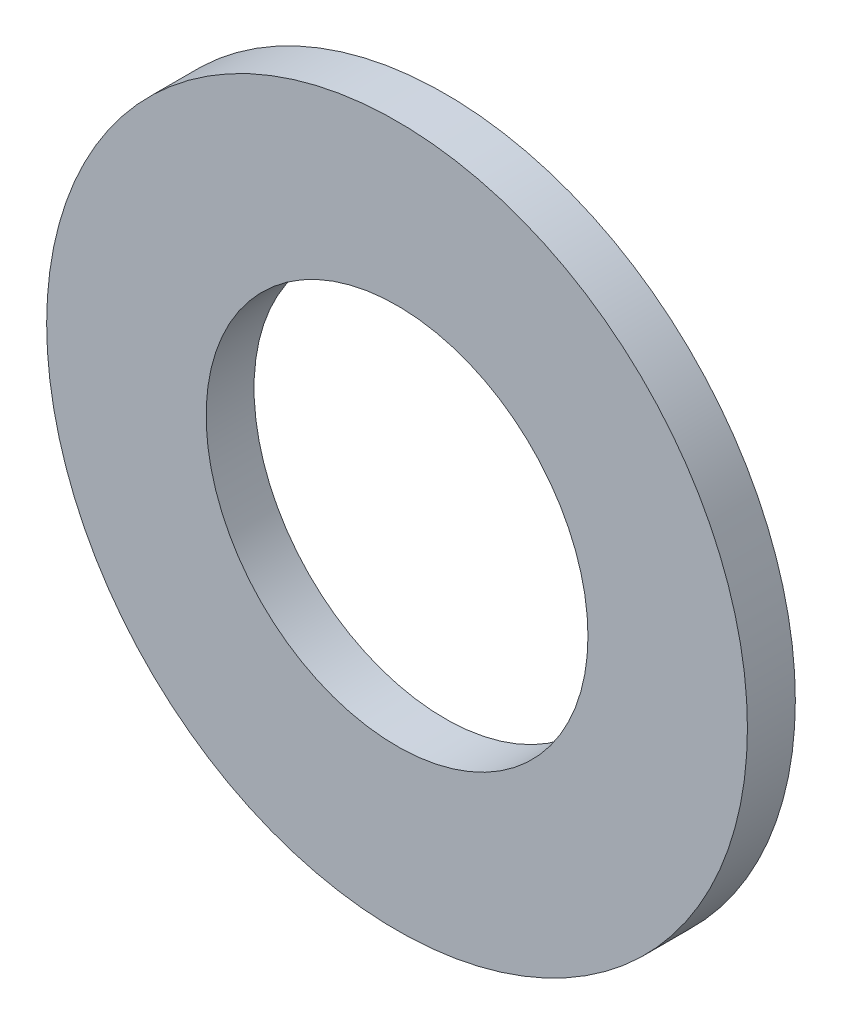
SolidWorks part; units mm, degrees
ref_plane "Front Plane" through (0, 0, 0) normal (0, 0, 1) x (1, 0, 0)
ref_plane "Top Plane" through (0, 0, 0) normal (0, 1, 0) x (1, 0, 0)
ref_plane "Right Plane" through (0, 0, 0) normal (1, 0, 0) x (0, 0, -1)
sketch "Sketch1" plane through (0, 0, 0) normal (0, 0, 1) x (1, 0, 0)
  line L0 (-5.9436, 0) -> (5.9436, 0) construction
  line L1 (0, -5.9436) -> (0, 5.9436) construction
  circle A0 centre (0, 0) radius 5.9436
  circle A1 centre (0, 0) radius 3.2385
  point P4 (0, 0)
  point P9 (0, 0)
  dimension "ID" = 6.477
  dimension "OD" = 11.8872
sketch "Sketch2" plane through (0, 0, 0) normal (1, 0, 0) x (0, 0, -1)
  line L0 (0.4064, 5.9436) -> (-0.4064, 5.9436) construction
  line L1 (0, 5.9436) -> (0, -5.9436) construction
  point P4 (0, 5.9436)
  dimension "Thickness" = 0.8128
sketch "Sketch3" plane through (0, 0, 0) normal (0, 0, 1) x (1, 0, 0)
  line L0 (0, -5.9436) -> (0, 5.9436) construction
  circle A0 centre (0, 0) radius 5.9436
  circle A1 centre (0, 0) radius 3.2385
  circle A2 centre (0, 0) radius 3.2385 construction
extrude "Boss-Extrude1" add sketch "Sketch3" along normal mid plane 0.8128
equation "\"D1@Boss-Extrude1\" = \"Thickness@Sketch2\""
